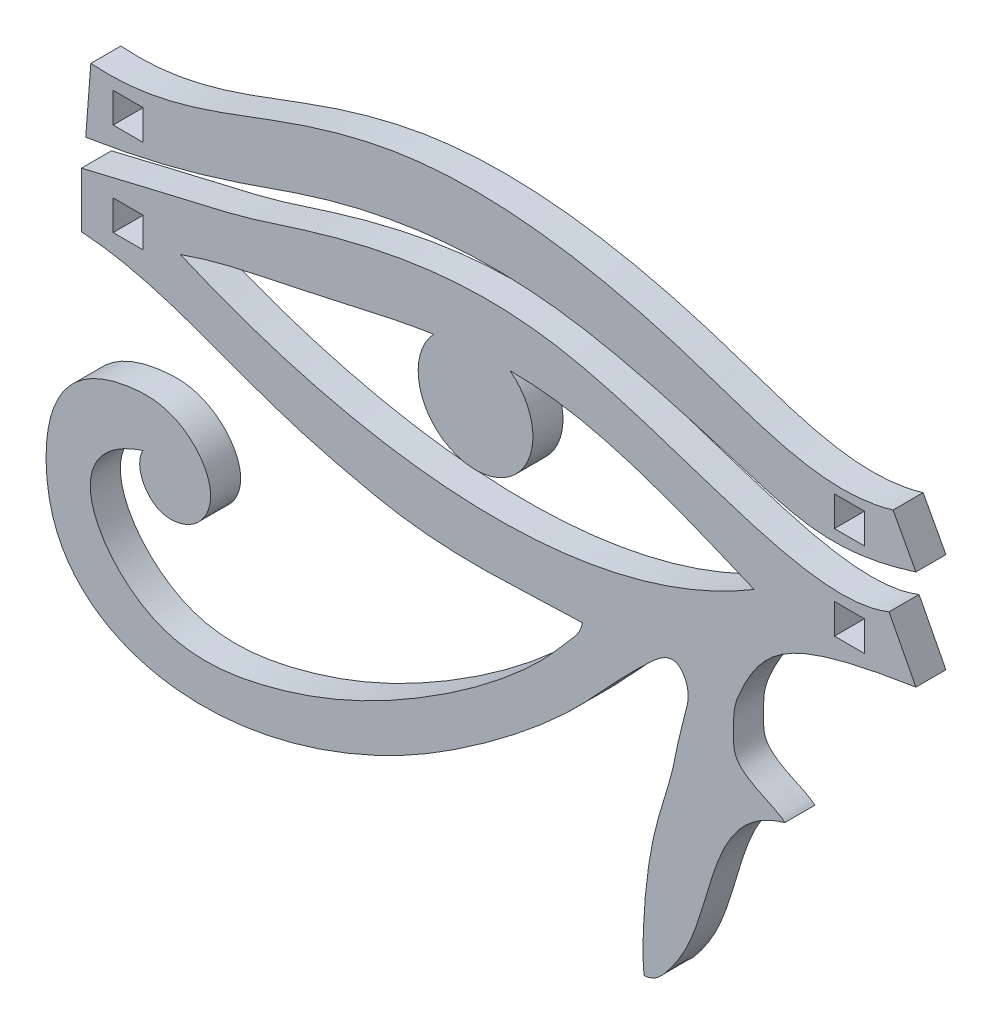
SolidWorks part; units mm, degrees
ref_plane "Front Plane" through (0, 0, 0) normal (0, 0, 1) x (1, 0, 0)
ref_plane "Top Plane" through (0, 0, 0) normal (0, 1, 0) x (1, 0, 0)
ref_plane "Right Plane" through (0, 0, 0) normal (1, 0, 0) x (0, 0, -1)
sketch "Sketch1" plane through (0, 0, 0) normal (0, 0, 1) x (1, 0, 0)
  line L0 (-45, 30) -> (45, -30) construction
  line L1 (-45, 30) -> (45, 30) construction
  line L2 (-45, 30) -> (-45, -30) construction
  line L3 (-45, -30) -> (45, -30) construction
  line L4 (45, 30) -> (45, -30) construction
  line L5 (45, 30) -> (0, 0) construction
  line L6 (0, 0) -> (-45, -30) construction
  line L7 (-34.5122, 17.4189) -> (-34.5122, 11.1189) construction
  line L8 (-37.5122, 20.4189) -> (-34.5122, 20.4189)
  line L9 (-37.5122, 20.4189) -> (-37.5122, 17.4189)
  line L10 (-37.5122, 17.4189) -> (-34.5122, 17.4189)
  line L11 (-34.5122, 20.4189) -> (-34.5122, 17.4189)
  line L12 (34.51, 21.5346) -> (37.51, 21.5346)
  line L13 (34.51, 21.5346) -> (34.51, 18.5346)
  line L14 (34.51, 18.5346) -> (37.51, 18.5346)
  line L15 (37.51, 21.5346) -> (37.51, 18.5346)
  line L16 (34.51, 12.2346) -> (37.51, 12.2346)
  line L17 (34.51, 12.2346) -> (34.51, 9.2346)
  line L18 (34.51, 9.2346) -> (37.51, 9.2346)
  line L19 (37.51, 12.2346) -> (37.51, 9.2346)
  line L20 (-37.5122, 11.1189) -> (-34.5122, 11.1189)
  line L21 (-37.5122, 11.1189) -> (-37.5122, 8.1189)
  line L22 (-37.5122, 8.1189) -> (-34.5122, 8.1189)
  line L23 (-34.5122, 11.1189) -> (-34.5122, 8.1189)
  line L24 (37.51, 18.5346) -> (37.51, 12.2346) construction
  line B0 (-39.7352, 21.6413) -> (-40.2472, 14.9973)
  line B1 (40.3665, 23.0709) -> (42.6459, 18.8495)
  line B2 (-40.6759, 12.1097) -> (-40.6759, 6.6116)
  line B3 (39.9636, 14.0632) -> (42.6459, 8.8912)
  circle B4 centre (-1.3241, 11.4176) radius 5.727
  spline B5 degree 3 poles (-39.7352, 21.6413) (-32.5681, 21.07) (-22.6531, 25.9746) (-2.6593, 31.3683) (18.1937, 27.7738) (33.4227, 21.004) (40.3665, 23.0709) knots 0 0 0 0 0.252986 0.399518 0.752994 1 1 1 1
  spline B6 degree 3 poles (-40.2472, 14.9973) (-34.6283, 15.874) (-27.5877, 17.6713) (-12.5397, 23.207) (4.9288, 25.6622) (26.2103, 18.8208) (34.9922, 16.3864) (42.6459, 18.8495) knots 0 0 0 0 0.19092 0.269409 0.566347 0.808779 1 1 1 1
  spline B7 degree 3 poles (-40.6759, 12.1097) (-35.8538, 13.3139) (-31.0387, 14.3501) (-23.5951, 16.1845) (-13.3445, 19.6903) (9.4969, 24.3867) (31.4682, 10.6061) (39.9636, 14.0632) knots 0 0 0 0 0.177934 0.205599 0.276648 0.570643 1 1 1 1
  spline B8 degree 3 poles (-30.7977, 9.5829) (-26.9926, 10.961) (-15.082, 13.0645) (4.6009, 18.7199) (19.784, 12.0429) (26.4988, 9.2671) knots 0 0 0 0 0.204187 0.621088 1 1 1 1
  spline B9 degree 3 poles (-30.7977, 9.5829) (-12.9437, 1.8574) (9.0425, -1.2643) (26.4988, 9.2671) knots 0 0 0 0 1 1 1 1
  spline B10 degree 3 poles (-40.6759, 6.6116) (-33.2561, 6.1512) (-24.7173, 1.7155) (-14.5288, -0.8555) (-3.8999, -3.1962) (2.9352, -2.3053) (9.3416, -2.1917) knots 0 0 0 0 0.402369 0.52197 0.581734 1 1 1 1
  spline B11 degree 3 poles (9.3416, -2.1917) (9.172, -3.231) (7.8789, -4.4942) (5.8209, -7.0115) (1.1775, -11.421) (-8.0209, -17.9738) (-20.1586, -23.6962) (-36.4369, -25.6284) (-43.6969, -12.257) (-34.5328, -9.2286) knots 0 0 0 0 0.043944 0.077471 0.143724 0.324672 0.571491 0.735829 1 1 1 1
  spline B12 degree 3 poles (-34.5328, -9.2286) (-35.4027, -10.8136) (-33.6695, -14.6021) (-28.8413, -13.3118) (-27.1148, -9.3947) (-29.376, -5.6184) (-32.6658, -4.2112) (-39.1711, -4.4179) (-44.8536, -7.7782) (-43.4146, -27.1542) (-28.1735, -31.5304) (-8.2481, -22.6724) (-1.1619, -18.1648) (4.3009, -13.9618) (10.2772, -8.4887) (12.369, -5.7089) (17.5275, -0.8708) (19.211, -0.6936) (20.1283, -2.8996) (19.3037, -5.9863) (18.8689, -7.7775) (18.2695, -10.9726) (17.4665, -13.4106) (15.4578, -20.3306) (15.2399, -27.7337) (15.4942, -29.6232) knots 0 0 0 0 0.060282 0.104631 0.143021 0.196105 0.239877 0.264242 0.420255 0.464597 0.663326 0.692484 0.73133 0.776341 0.787878 0.840161 0.847806 0.8578 0.869419 0.873546 0.896236 0.901935 0.924829 0.934922 1 1 1 1
  spline B13 degree 3 poles (15.4942, -29.6232) (16.5656, -29.572) (18.1609, -27.83) (22.6323, -20.6311) (22.3028, -11.3922) (29.5589, -9.3675) knots 0 0 0 0 0.11596 0.26146 1 1 1 1
  spline B14 degree 3 poles (29.5589, -9.3675) (28.4976, -8.3549) (24.3564, -7.5199) (24.4679, -4.0515) (24.3844, -1.9272) (27.2902, 4.8299) (30.4053, 6.9662) (42.6459, 8.8912) knots 0 0 0 0 0.19515 0.243888 0.314831 0.390443 1 1 1 1
  dimension "D1" = 90
  dimension "D2" = 60
  dimension "D3" = 3
  dimension "D4" = 6.3
  dimension "D5" = 34.51
  dimension "D6" = 34.5122
  dimension "D7" = 8.1189
  dimension "D8" = 9.2346
sketch_block_instance "Block4-1"
sketch_block "Block4"
extrude "Boss-Extrude2" add sketch "Sketch1" along normal blind 3 contours B0 B6 B1 B5 L12 L15 L14 L13 L8 L11 L10 L9 | B13 B14 B3 B7 B2 B10 B11 B12 L20 L23 L22 L21 L16 L19 L18 L17 B9 B8 B4 | B8 B4 | B4 B8
